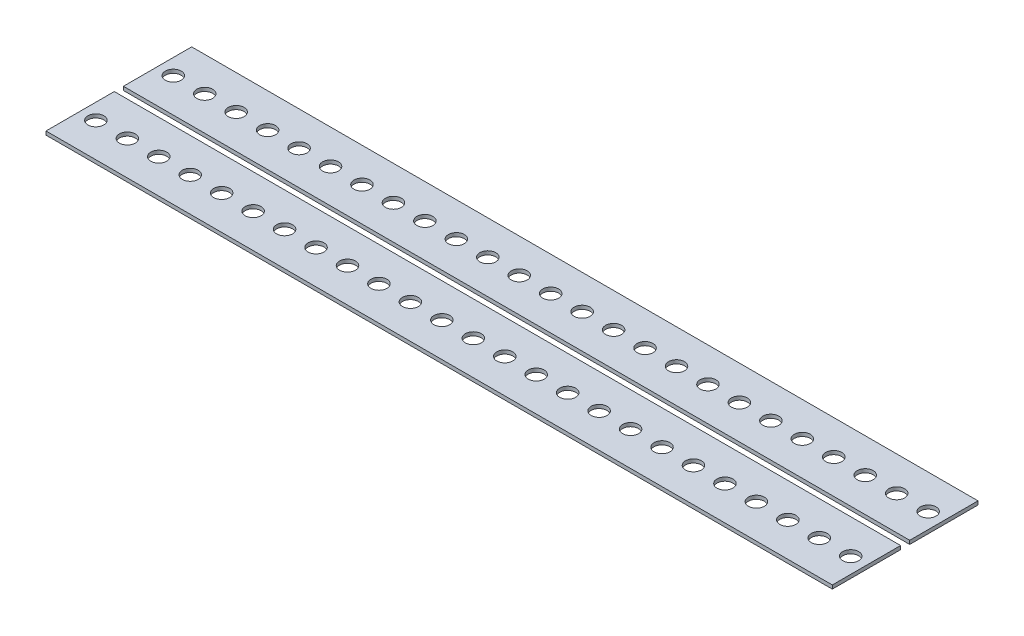
SolidWorks part; units mm, degrees
ref_plane "Front Plane" through (0, 0, 0) normal (0, 0, 1) x (1, 0, 0)
ref_plane "Top Plane" through (0, 0, 0) normal (0, 1, 0) x (1, 0, 0)
ref_plane "Right Plane" through (0, 0, 0) normal (1, 0, 0) x (0, 0, -1)
sketch "Sketch1" plane through (0, 0, 0) normal (0, 1, 0) x (1, 0, 0)
  line L1 (-3.4545, -7.5) -> (3.4545, -7.5)
  line L2 (-3.4545, -7.5) -> (-3.4545, 7.5)
  line L3 (-3.4545, 7.5) -> (3.4545, 7.5)
  line L4 (3.4545, -7.5) -> (3.4545, 7.5)
  line L5 (-3.4545, -7.5) -> (3.4545, 7.5) construction
  line L6 (-3.4545, 7.5) -> (3.4545, -7.5) construction
  circle A0 centre (0, 0) radius 1.75
  point P0 (0, 0)
  dimension "D1" = 3.5
  dimension "D2" = 6.909
  dimension "D3" = 15
extrude "Boss-Extrude1" add sketch "Sketch1" along normal blind 0.8
pattern_linear "LPattern1" count 25 spacing 6.909 along (-1, 0, 0) of "Boss-Extrude1"
pattern_linear "LPattern2" count 2 spacing 17 along (0, 0, -1) of bodies 102
equation "\"D2@Sketch1\"= 6.90897887mm"
equation "\"D3@LPattern1\"=\"D2@Sketch1\""
